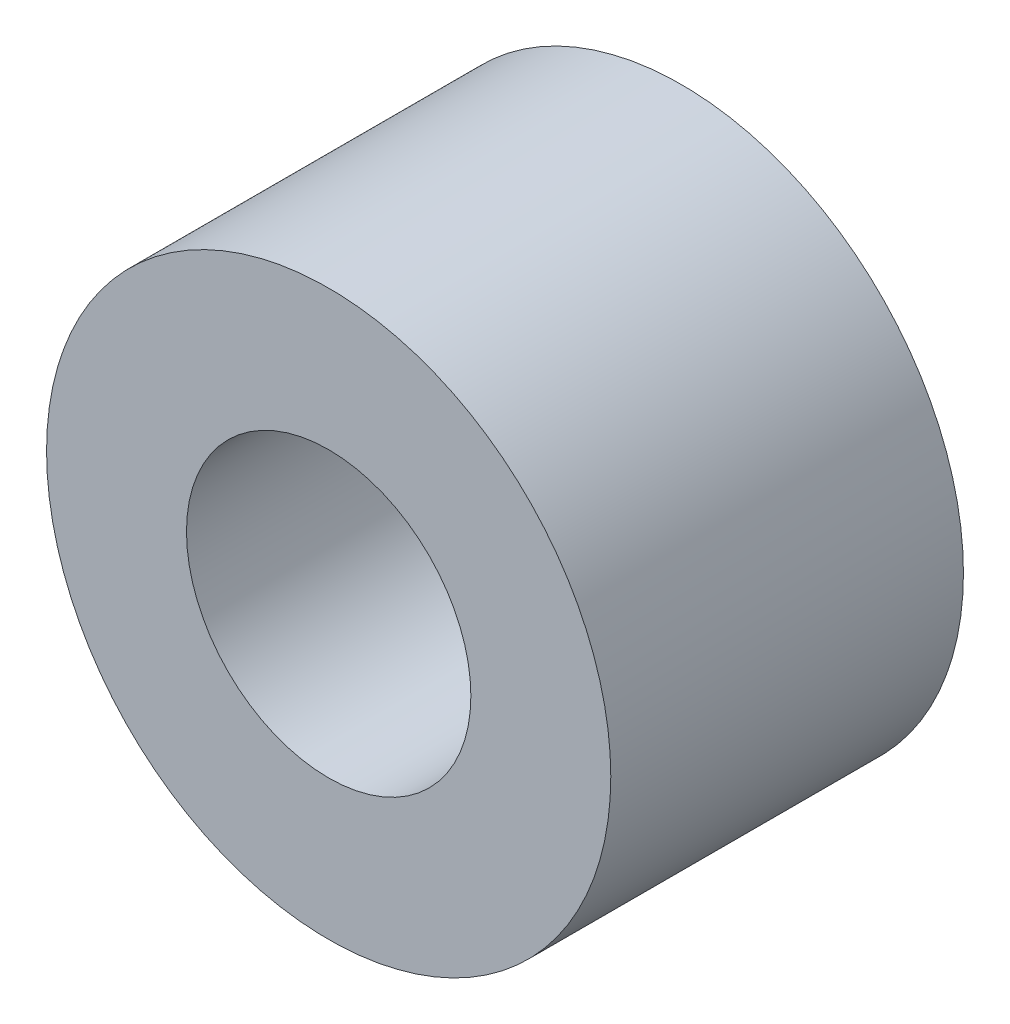
SolidWorks part; units mm, degrees
ref_plane "Front Plane" through (0, 0, 0) normal (0, 0, 1) x (1, 0, 0)
ref_plane "Top Plane" through (0, 0, 0) normal (0, 1, 0) x (1, 0, 0)
ref_plane "Right Plane" through (0, 0, 0) normal (1, 0, 0) x (0, 0, -1)
sketch "Sketch1" plane through (0, 0, 0) normal (0, 0, 1) x (1, 0, 0)
  circle A0 centre (0, 0) radius 6.35
  circle A1 centre (0, 0) radius 3.2004
  dimension "OD" = 12.7
  dimension "ID" = 6.4008
extrude "Extrude1" add sketch "Sketch1" along normal mid plane 7.9375
sketch "Sketch2" plane through (0, 0, 0) normal (1, 0, 0) x (0, 0, -1)
  line L0 (-3.9688, -3.2004) -> (3.9688, -3.2004) construction
  line L3 (3.9688, 3.2004) -> (-3.9688, 3.2004) construction
  line L5 (-3.9688, -3.2004) -> (3.9688, -3.2004)
  line L6 (3.9688, 3.2004) -> (-3.9688, 3.2004)
sketch "Sketch4" plane through (0, 0, 3.9688) normal (0, 0, 1) x (1, 0, 0)
  line L0 (0, 0) -> (-2.263, 2.263)
  line L1 (0, -3.4925) -> (0, 3.4925) construction
  circle A0 centre (0, 0) radius 3.2004 construction
  dimension "D1" = 45
